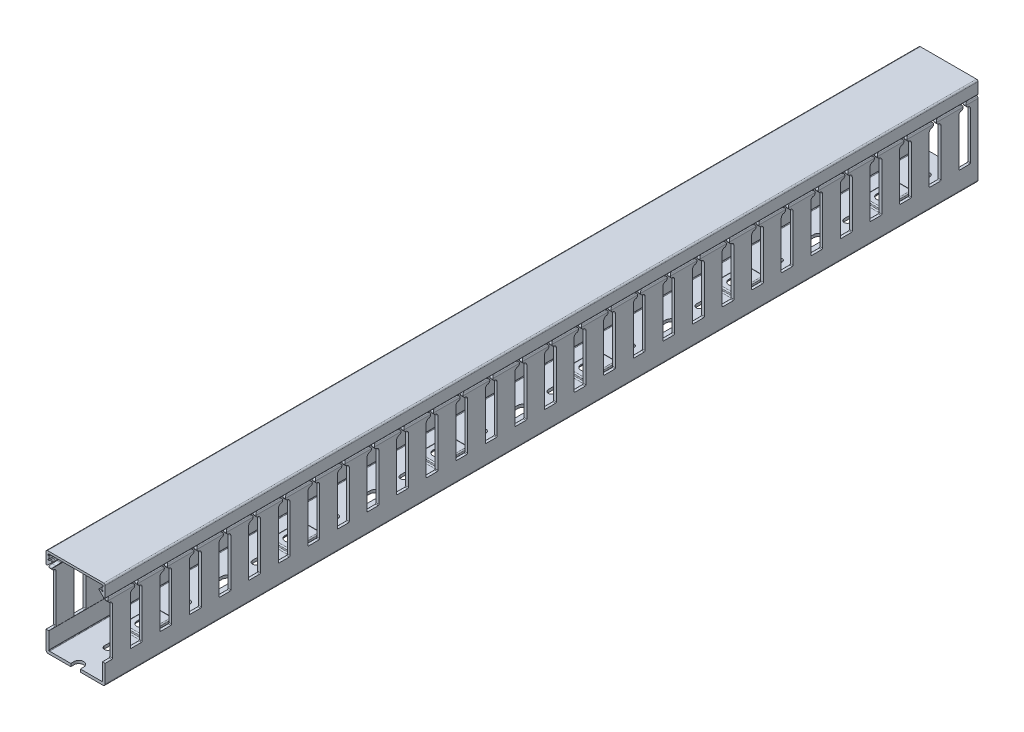
SolidWorks part; units mm, degrees
ref_plane "Front Plane" through (0, 0, 0) normal (0, 0, 1) x (1, 0, 0)
ref_plane "Top Plane" through (0, 0, 0) normal (0, 1, 0) x (1, 0, 0)
ref_plane "Right Plane" through (0, 0, 0) normal (1, 0, 0) x (0, 0, -1)
sketch "Sketch1" plane through (0, 0, 0) normal (0, 0, 1) x (1, 0, 0)
  line L0 (-18.2, -27.85) -> (-17.973, -27.983)
  line L1 (-20, -28.55) -> (-20, 19.1871)
  line L2 (-20, 21.7598) -> (-20, 29.05)
  line L3 (-18.5, 28.35) -> (-18.5, 27.55)
  line L4 (-18.5, 25.25) -> (-18.5, 25.058)
  line L5 (-19.6147, 20.1908) -> (-15.6798, 24.5609)
  line L6 (-17.8221, 24.7703) -> (-17.3671, 25.2097)
  line L7 (-15.9527, 24.4903) -> (-19.1527, 21.4001)
  line L8 (-18.1, 18.8416) -> (-18.1, -16.3923)
  line L9 (-18.1, -16.5077) -> (-18.1, -27.65)
  line L10 (-18, 25.55) -> (-18, 27.25)
  line L11 (-14.8603, 22.6316) -> (-17.9716, 19.1762)
  line L12 (-18.2, -16.45) -> (-18.1, -16.5077)
  line L13 (-13.3, 25.85) -> (-13.3, 24.6071)
  line L14 (-7, -28.15) -> (-7, -25.65)
  line L15 (-18.5, -30.05) -> (18.5, -30.05)
  line L16 (0, -30.05) -> (0, 30.05) construction
  line L18 (-17.6, -28.15) -> (17.6, -28.15)
  line L19 (-17.973, -27.983) -> (-17.973, -27.7208) construction
  line L20 (-18.082, -27.7829) -> (-17.973, -27.7208) construction
  line L21 (18.1, -16.5077) -> (18.1, -16.3923) construction
  line L23 (-7, -25.65) -> (7, -25.65)
  line L24 (-18.1, -16.5077) -> (-18.1, -16.3923) construction
  line L25 (-2.25, -30.05) -> (-2.25, -28.15)
  line L26 (2.25, -30.05) -> (2.25, -28.15)
  line L27 (7, -28.15) -> (7, -25.65)
  line L28 (17.973, -27.717) -> (18.082, -27.7829) construction
  line L29 (-18.1, -16.3923) -> (-18.2, -16.45)
  line L30 (18.1, -16.3923) -> (18.2, -16.45)
  line L31 (-18.082, -27.7829) -> (-18.2, -27.85)
  line L33 (18.4, 25.35) -> (18.2, 25.35)
  line L34 (-16.3, 25.35) -> (-17.0198, 25.35)
  line L35 (-18.4, 25.35) -> (-18.2, 25.35)
  line L36 (16.3, 25.35) -> (17.0198, 25.35)
  line L38 (-18.2, 27.45) -> (-18.4, 27.45)
  line L39 (18.2, 27.45) -> (18.4, 27.45)
  line L40 (16.0883, 27.65) -> (15.1, 27.65)
  line L41 (-16.0883, 27.65) -> (-15.1, 27.65)
  line L42 (-18.3, 28.55) -> (18.3, 28.55)
  line L44 (19, 30.05) -> (-19, 30.05)
  line L46 (-16.3812, 25.7055) -> (-17.6188, 25.3739)
  line L47 (16.3812, 25.7055) -> (17.6188, 25.3739)
  line L48 (13.3, 25.85) -> (13.3, 24.6071)
  line L49 (18, 25.55) -> (18, 27.25)
  line L50 (18.1, 18.8416) -> (18.1, -16.3923)
  line L51 (18.1, -16.5077) -> (18.1, -27.65)
  line L52 (18.5, 28.35) -> (18.5, 27.55)
  line L53 (18.5, 25.25) -> (18.5, 25.058)
  line L54 (18.2, -16.45) -> (18.1, -16.5077)
  line L55 (14.8603, 22.6316) -> (17.9716, 19.1762)
  line L56 (20, -28.55) -> (20, 19.1871)
  line L57 (20, 21.7598) -> (20, 29.05)
  line L58 (15.9527, 24.4903) -> (19.1527, 21.4001)
  line L59 (17.8221, 24.7703) -> (17.3671, 25.2097)
  line L60 (19.6147, 20.1908) -> (15.6798, 24.5609)
  line L61 (18.2, -27.85) -> (17.973, -27.983)
  line L62 (-2.25, -29.1) -> (2.25, -29.1) construction
  line L63 (-7, -26.9) -> (7, -26.9) construction
  line L64 (0, -29.1) -> (0, -26.9) construction
  line L68 (17.973, -27.983) -> (17.973, -27.717) construction
  line L69 (20, -4.6815) -> (18.1, -4.6815) construction
  line L70 (-20, -4.6815) -> (-18.1, -4.6815) construction
  line L71 (18.082, -27.7829) -> (18.2, -27.85)
  line L72 (16.4159, 20.9039) -> (17.8279, 22.1752) construction
  line L73 (18.2, -27.85) -> (17.973, -27.85) construction
  line L74 (20, 19.1871) -> (20, 19.7629) construction
  line L75 (20, 19.7629) -> (19.6147, 20.1908) construction
  line L76 (18.1, 18.8416) -> (18.1, 19.0335) construction
  line L77 (18.1, 19.0335) -> (17.9716, 19.1762) construction
  line L78 (20, 21.7598) -> (20, 20.5819) construction
  line L79 (20, 20.5819) -> (19.1527, 21.4001) construction
  line L80 (18.3, 28.55) -> (18.3, 30.05) construction
  line L81 (18.5, 28.35) -> (20, 28.35) construction
  line L82 (17.5946, 24.99) -> (16.5526, 23.911) construction
  line L83 (14.0985, 26.3171) -> (16.3812, 25.7055) construction
  line L84 (14.0985, 26.3171) -> (15.6798, 24.5609) construction
  line L85 (15.1, 24.6071) -> (15.1, 25.85) construction
  line L86 (15.1, 25.85) -> (16.0883, 25.85) construction
  line L87 (16.0883, 25.85) -> (16.0883, 24.6071) construction
  line L88 (16.0883, 24.6071) -> (15.1, 24.6071) construction
  arc A0 (-20, -28.55) -> (-18.5, -30.05) centre (-18.5, -28.55) ccw
  arc A1 (-18.1, -27.65) -> (-18.082, -27.7829) centre (-17.6, -27.65) ccw
  arc A2 (-17.973, -27.983) -> (-17.6, -28.15) centre (-17.6, -27.65) ccw
  arc A3 (-17.5208, 26.94) -> (-18.1276, 26.6686) centre (-15.7875, 22.25) ccw
  arc A4 (-14.8603, 22.6316) -> (-13.7623, 23.4026) centre (-15.9918, 25.41) ccw
  arc A5 (-16.0883, 27.65) -> (-17.5208, 26.94) centre (-16.0883, 25.85) ccw
  arc A6 (-13.3, 25.85) -> (-15.1, 27.65) centre (-15.1, 25.85) ccw
  arc A7 (-13.7623, 23.4026) -> (-13.3, 24.6071) centre (-15.1, 24.6071) ccw
  arc A8 (-19.6147, 20.1908) -> (-20, 19.1871) centre (-18.5, 19.1871) ccw
  arc A9 (-19, 30.05) -> (-20, 29.05) centre (-19, 29.05) ccw
  arc A10 (-15.6798, 24.5609) -> (-16.3812, 25.7055) centre (-16.2, 25.0293) ccw
  arc A11 (-18.1276, 26.6686) -> (-17.6188, 25.3739) centre (-17.8, 26.05) ccw
  arc A12 (-17.0198, 25.35) -> (-17.3671, 25.2097) centre (-17.0198, 24.85) ccw
  arc A13 (-15.9527, 24.4903) -> (-16.3, 25.35) centre (-16.3, 24.85) ccw
  arc A14 (-20, 21.7598) -> (-19.1527, 21.4001) centre (-19.5, 21.7598) ccw
  arc A15 (-17.9716, 19.1762) -> (-18.1, 18.8416) centre (-17.6, 18.8416) ccw
  arc A16 (-18.5, 25.058) -> (-17.8221, 24.7703) centre (-18.1, 25.058) ccw
  arc A17 (-18.3, 28.55) -> (-18.5, 28.35) centre (-18.3, 28.35) ccw
  arc A18 (-18, 27.25) -> (-18.2, 27.45) centre (-18.2, 27.25) ccw
  arc A19 (-18.2, 25.35) -> (-18, 25.55) centre (-18.2, 25.55) ccw
  arc A20 (-18.4, 25.35) -> (-18.5, 25.25) centre (-18.4, 25.25) ccw
  arc A21 (-18.5, 27.55) -> (-18.4, 27.45) centre (-18.4, 27.55) ccw
  arc A22 (18.5, -30.05) -> (20, -28.55) centre (18.5, -28.55) ccw
  arc A23 (17.6, -28.15) -> (17.973, -27.983) centre (17.6, -27.65) ccw
  arc A24 (18.082, -27.7829) -> (18.1, -27.65) centre (17.6, -27.65) ccw
  arc A25 (18.1276, 26.6686) -> (17.5208, 26.94) centre (15.7875, 22.25) ccw
  arc A26 (13.7623, 23.4026) -> (14.8603, 22.6316) centre (15.9918, 25.41) ccw
  arc A27 (13.3, 24.6071) -> (13.7623, 23.4026) centre (15.1, 24.6071) ccw
  arc A28 (15.1, 27.65) -> (13.3, 25.85) centre (15.1, 25.85) ccw
  arc A29 (17.5208, 26.94) -> (16.0883, 27.65) centre (16.0883, 25.85) ccw
  arc A30 (20, 19.1871) -> (19.6147, 20.1908) centre (18.5, 19.1871) ccw
  arc A31 (20, 29.05) -> (19, 30.05) centre (19, 29.05) ccw
  arc A32 (17.6188, 25.3739) -> (18.1276, 26.6686) centre (17.8, 26.05) ccw
  arc A33 (16.3812, 25.7055) -> (15.6798, 24.5609) centre (16.2, 25.0293) ccw
  arc A34 (17.3671, 25.2097) -> (17.0198, 25.35) centre (17.0198, 24.85) ccw
  arc A35 (16.3, 25.35) -> (15.9527, 24.4903) centre (16.3, 24.85) ccw
  arc A36 (19.1527, 21.4001) -> (20, 21.7598) centre (19.5, 21.7598) ccw
  arc A37 (18.1, 18.8416) -> (17.9716, 19.1762) centre (17.6, 18.8416) ccw
  arc A38 (17.8221, 24.7703) -> (18.5, 25.058) centre (18.1, 25.058) ccw
  arc A39 (18.5, 28.35) -> (18.3, 28.55) centre (18.3, 28.35) ccw
  arc A40 (18.2, 27.45) -> (18, 27.25) centre (18.2, 27.25) ccw
  arc A41 (18, 25.55) -> (18.2, 25.35) centre (18.2, 25.55) ccw
  arc A42 (18.5, 25.25) -> (18.4, 25.35) centre (18.4, 25.25) ccw
  arc A43 (18.4, 27.45) -> (18.5, 27.55) centre (18.4, 27.55) ccw
  point P188 (0, 28.55)
  dimension "D2" = 1.5
  dimension "D9" = 0.5
  dimension "D12" = 1
  dimension "D13" = 1.8
  dimension "D14" = 0.2
  dimension "D15" = 0.1
  dimension "D16" = 0.7
  dimension "D28" = 0.4
  dimension "D29" = 3
  dimension "D30" = 5
  dimension "D1" = 14
  dimension "Height" = 60.1
  dimension "Width" = 40
  dimension "D3" = 1.9
  dimension "D4" = 1.5
  dimension "D5" = 0.1155
  dimension "D6" = 46
  dimension "D7" = 138
  dimension "D10" = 2.5
  dimension "D11" = 4.5
  dimension "D18" = 0.3
  dimension "D19" = 0.266
  dimension "D20" = 60
  dimension "D21" = 8.6165
  dimension "D22" = 9.4681
  dimension "D23" = 0.5
  dimension "D24" = 1.1
  dimension "D25" = 2.1
  dimension "D26" = 0.9
  dimension "D27" = 4.8
  dimension "D31" = 0.9883
  dimension "D32" = 1.2429
  dimension "D33" = 33
  dimension "D34" = 5.0184
  dimension "D35" = 4.2208
  dimension "Slot Height" = 13.6
sketch "Sketch2" plane through (0, 0, 0) normal (0, 1, 0) x (1, 0, 0)
  line L1 (-20, 295) -> (20, 295)
  line L2 (-20, 295) -> (-20, -295)
  line L3 (-20, -295) -> (20, -295)
  line L4 (20, 295) -> (20, -295)
  line L5 (-20, 295) -> (20, -295) construction
  line L6 (-20, -295) -> (20, 295) construction
  line L9 (0, -300.25) -> (0, -292.75) construction
  line L10 (-3.25, -300.25) -> (-3.25, -292.75)
  line L11 (3.25, -300.25) -> (3.25, -292.75)
  line L15 (0, -289.5) -> (0, -292.75) construction
  line L16 (0, -300.25) -> (0, -303.5) construction
  line L17 (0, -273.25) -> (0, -269.75) construction
  line L18 (-2.25, -273.25) -> (-2.25, -269.75)
  line L19 (2.25, -273.25) -> (2.25, -269.75)
  line L23 (0, -273.25) -> (0, -275.5) construction
  line L24 (0, -250.25) -> (0, -242.75) construction
  line L26 (0, -269.75) -> (0, -267.5) construction
  line L30 (7, -257.2071) -> (-7, -257.2071)
  line L31 (7, -257.2071) -> (7, -235.7929)
  line L32 (7, -235.7929) -> (-7, -235.7929)
  line L33 (-7, -257.2071) -> (-7, -235.7929)
  line L34 (-3.25, -250.25) -> (-3.25, -242.75)
  line L35 (3.25, -250.25) -> (3.25, -242.75)
  line L36 (0, -200.25) -> (0, -192.75) construction
  line L37 (-3.25, -200.25) -> (-3.25, -192.75)
  line L38 (3.25, -200.25) -> (3.25, -192.75)
  line L45 (0, -223.25) -> (0, -219.75) construction
  line L46 (-2.25, -223.25) -> (-2.25, -219.75)
  line L47 (2.25, -223.25) -> (2.25, -219.75)
  arc A2 (-3.25, -300.25) -> (3.25, -300.25) centre (0, -300.25) ccw
  arc A3 (3.25, -292.75) -> (-3.25, -292.75) centre (0, -292.75) ccw
  arc A6 (-2.25, -273.25) -> (2.25, -273.25) centre (0, -273.25) ccw
  arc A7 (2.25, -269.75) -> (-2.25, -269.75) centre (0, -269.75) ccw
  arc A10 (-3.25, -250.25) -> (3.25, -250.25) centre (0, -250.25) ccw
  arc A11 (3.25, -242.75) -> (-3.25, -242.75) centre (0, -242.75) ccw
  arc A12 (-3.25, -200.25) -> (3.25, -200.25) centre (0, -200.25) ccw
  arc A13 (3.25, -192.75) -> (-3.25, -192.75) centre (0, -192.75) ccw
  arc A18 (-2.25, -223.25) -> (2.25, -223.25) centre (0, -223.25) ccw
  arc A19 (2.25, -219.75) -> (-2.25, -219.75) centre (0, -219.75) ccw
  point P0 (0, 0)
  point P14 (0, -296.5)
  point P33 (0, -271.5)
  point P67 (0, -246.5)
  point P74 (-7, -246.5)
  point P75 (0, -196.5)
  point P96 (0, -221.5)
  dimension "D1" = 5.5
  dimension "D2" = 14
  dimension "Length" = 590
  dimension "D3" = 6.5
  dimension "D4" = 8
  dimension "D5" = 23.5
  dimension "D6" = 21.4142
  dimension "D7" = 25
  dimension "Slot Spacing 2" = 100
  dimension "Slot Spacing 1" = 50
sketch "Sketch3" plane through (0, 0, 0) normal (0, 0, 1) x (1, 0, 0)
  line L0 (15.9527, 24.4903) -> (19.1527, 21.4001) construction
  line L1 (16.3, 25.35) -> (17.0198, 25.35) construction
  line L2 (17.8221, 24.7703) -> (17.3671, 25.2097) construction
  line L3 (18.5, 25.25) -> (18.5, 25.058) construction
  line L4 (18.4, 25.35) -> (18.2, 25.35) construction
  line L5 (18, 25.55) -> (18, 27.25) construction
  line L6 (18.2, 27.45) -> (18.4, 27.45) construction
  line L7 (18.5, 28.35) -> (18.5, 27.55) construction
  line L8 (20, 21.7598) -> (20, 29.05) construction
  line L9 (19, 30.05) -> (-19, 30.05) construction
  line L10 (-18.3, 28.55) -> (18.3, 28.55) construction
  line L11 (-18.5, 28.35) -> (-18.5, 27.55) construction
  line L12 (-18.2, 27.45) -> (-18.4, 27.45) construction
  line L13 (-18, 25.55) -> (-18, 27.25) construction
  line L14 (-18.4, 25.35) -> (-18.2, 25.35) construction
  line L15 (-18.5, 25.25) -> (-18.5, 25.058) construction
  line L16 (-17.8221, 24.7703) -> (-17.3671, 25.2097) construction
  line L17 (-16.3, 25.35) -> (-17.0198, 25.35) construction
  line L18 (-15.9527, 24.4903) -> (-19.1527, 21.4001) construction
  line L19 (-20, 21.7598) -> (-20, 29.05) construction
  line L20 (15.9527, 24.4903) -> (19.1527, 21.4001)
  line L21 (16.3, 25.35) -> (17.0198, 25.35)
  line L22 (17.8221, 24.7703) -> (17.3671, 25.2097)
  line L23 (18.5, 25.25) -> (18.5, 25.058)
  line L24 (18.4, 25.35) -> (18.2, 25.35)
  line L25 (18, 25.55) -> (18, 27.25)
  line L26 (18.2, 27.45) -> (18.4, 27.45)
  line L27 (18.5, 28.35) -> (18.5, 27.55)
  line L28 (20, 21.7598) -> (20, 29.05)
  line L29 (19, 30.05) -> (-19, 30.05)
  line L30 (-18.3, 28.55) -> (18.3, 28.55)
  line L31 (-18.5, 28.35) -> (-18.5, 27.55)
  line L32 (-18.2, 27.45) -> (-18.4, 27.45)
  line L33 (-18, 25.55) -> (-18, 27.25)
  line L34 (-18.4, 25.35) -> (-18.2, 25.35)
  line L35 (-18.5, 25.25) -> (-18.5, 25.058)
  line L36 (-17.8221, 24.7703) -> (-17.3671, 25.2097)
  line L37 (-16.3, 25.35) -> (-17.0198, 25.35)
  line L38 (-15.9527, 24.4903) -> (-19.1527, 21.4001)
  line L39 (-20, 21.7598) -> (-20, 29.05)
  arc A0 (19.1527, 21.4001) -> (20, 21.7598) centre (19.5, 21.7598) ccw construction
  arc A1 (16.3, 25.35) -> (15.9527, 24.4903) centre (16.3, 24.85) ccw construction
  arc A2 (17.3671, 25.2097) -> (17.0198, 25.35) centre (17.0198, 24.85) ccw construction
  arc A3 (17.8221, 24.7703) -> (18.5, 25.058) centre (18.1, 25.058) ccw construction
  arc A4 (18.5, 25.25) -> (18.4, 25.35) centre (18.4, 25.25) ccw construction
  arc A5 (18, 25.55) -> (18.2, 25.35) centre (18.2, 25.55) ccw construction
  arc A6 (18.2, 27.45) -> (18, 27.25) centre (18.2, 27.25) ccw construction
  arc A7 (18.4, 27.45) -> (18.5, 27.55) centre (18.4, 27.55) ccw construction
  arc A8 (18.5, 28.35) -> (18.3, 28.55) centre (18.3, 28.35) ccw construction
  arc A9 (20, 29.05) -> (19, 30.05) centre (19, 29.05) ccw construction
  arc A10 (-18.3, 28.55) -> (-18.5, 28.35) centre (-18.3, 28.35) ccw construction
  arc A11 (-18.5, 27.55) -> (-18.4, 27.45) centre (-18.4, 27.55) ccw construction
  arc A12 (-18, 27.25) -> (-18.2, 27.45) centre (-18.2, 27.25) ccw construction
  arc A13 (-18.2, 25.35) -> (-18, 25.55) centre (-18.2, 25.55) ccw construction
  arc A14 (-18.4, 25.35) -> (-18.5, 25.25) centre (-18.4, 25.25) ccw construction
  arc A15 (-18.5, 25.058) -> (-17.8221, 24.7703) centre (-18.1, 25.058) ccw construction
  arc A16 (-17.0198, 25.35) -> (-17.3671, 25.2097) centre (-17.0198, 24.85) ccw construction
  arc A17 (-15.9527, 24.4903) -> (-16.3, 25.35) centre (-16.3, 24.85) ccw construction
  arc A18 (-20, 21.7598) -> (-19.1527, 21.4001) centre (-19.5, 21.7598) ccw construction
  arc A19 (-19, 30.05) -> (-20, 29.05) centre (-19, 29.05) ccw construction
  arc A20 (19.1527, 21.4001) -> (20, 21.7598) centre (19.5, 21.7598) ccw
  arc A21 (16.3, 25.35) -> (15.9527, 24.4903) centre (16.3, 24.85) ccw
  arc A22 (17.3671, 25.2097) -> (17.0198, 25.35) centre (17.0198, 24.85) ccw
  arc A23 (17.8221, 24.7703) -> (18.5, 25.058) centre (18.1, 25.058) ccw
  arc A24 (18.5, 25.25) -> (18.4, 25.35) centre (18.4, 25.25) ccw
  arc A25 (18, 25.55) -> (18.2, 25.35) centre (18.2, 25.55) ccw
  arc A26 (18.2, 27.45) -> (18, 27.25) centre (18.2, 27.25) ccw
  arc A27 (18.4, 27.45) -> (18.5, 27.55) centre (18.4, 27.55) ccw
  arc A28 (18.5, 28.35) -> (18.3, 28.55) centre (18.3, 28.35) ccw
  arc A29 (20, 29.05) -> (19, 30.05) centre (19, 29.05) ccw
  arc A30 (-18.3, 28.55) -> (-18.5, 28.35) centre (-18.3, 28.35) ccw
  arc A31 (-18.5, 27.55) -> (-18.4, 27.45) centre (-18.4, 27.55) ccw
  arc A32 (-18, 27.25) -> (-18.2, 27.45) centre (-18.2, 27.25) ccw
  arc A33 (-18.2, 25.35) -> (-18, 25.55) centre (-18.2, 25.55) ccw
  arc A34 (-18.4, 25.35) -> (-18.5, 25.25) centre (-18.4, 25.25) ccw
  arc A35 (-18.5, 25.058) -> (-17.8221, 24.7703) centre (-18.1, 25.058) ccw
  arc A36 (-17.0198, 25.35) -> (-17.3671, 25.2097) centre (-17.0198, 24.85) ccw
  arc A37 (-15.9527, 24.4903) -> (-16.3, 25.35) centre (-16.3, 24.85) ccw
  arc A38 (-20, 21.7598) -> (-19.1527, 21.4001) centre (-19.5, 21.7598) ccw
  arc A39 (-19, 30.05) -> (-20, 29.05) centre (-19, 29.05) ccw
extrude "Boss-Extrude1" add sketch "Sketch3" along normal up to vertex (295 mm away) from vertex at -295 separate body starting at point (20, 0, -295)
sketch "Sketch4" plane through (0, 0, 0) normal (0, 0, 1) x (1, 0, 0)
  line L0 (18.2, -27.85) -> (17.973, -27.983) construction
  line L1 (18.082, -27.7829) -> (18.2, -27.85) construction
  line L2 (18.1, -16.5077) -> (18.1, -27.65) construction
  line L3 (18.2, -16.45) -> (18.1, -16.5077) construction
  line L4 (18.1, -16.3923) -> (18.2, -16.45) construction
  line L5 (20, -28.55) -> (20, 19.1871) construction
  line L6 (18.1, 18.8416) -> (18.1, -16.3923) construction
  line L7 (19.6147, 20.1908) -> (15.6798, 24.5609) construction
  line L8 (16.3812, 25.7055) -> (17.6188, 25.3739) construction
  line L9 (14.8603, 22.6316) -> (17.9716, 19.1762) construction
  line L10 (13.3, 25.85) -> (13.3, 24.6071) construction
  line L11 (16.0883, 27.65) -> (15.1, 27.65) construction
  line L12 (-16.3812, 25.7055) -> (-17.6188, 25.3739) construction
  line L13 (-16.0883, 27.65) -> (-15.1, 27.65) construction
  line L14 (-13.3, 25.85) -> (-13.3, 24.6071) construction
  line L15 (-19.6147, 20.1908) -> (-15.6798, 24.5609) construction
  line L16 (-14.8603, 22.6316) -> (-17.9716, 19.1762) construction
  line L17 (-18.1, 18.8416) -> (-18.1, -16.3923) construction
  line L18 (-18.1, -16.3923) -> (-18.2, -16.45) construction
  line L19 (-18.2, -16.45) -> (-18.1, -16.5077) construction
  line L20 (-18.1, -16.5077) -> (-18.1, -27.65) construction
  line L21 (-18.082, -27.7829) -> (-18.2, -27.85) construction
  line L22 (-18.2, -27.85) -> (-17.973, -27.983) construction
  line L23 (-17.6, -28.15) -> (17.6, -28.15) construction
  line L24 (-18.5, -30.05) -> (18.5, -30.05) construction
  line L25 (-20, -28.55) -> (-20, 19.1871) construction
  line L26 (18.2, -27.85) -> (17.973, -27.983)
  line L27 (18.082, -27.7829) -> (18.2, -27.85)
  line L28 (18.1, -16.5077) -> (18.1, -27.65)
  line L29 (18.2, -16.45) -> (18.1, -16.5077)
  line L30 (18.1, -16.3923) -> (18.2, -16.45)
  line L31 (20, -28.55) -> (20, 19.1871)
  line L32 (18.1, 18.8416) -> (18.1, -16.3923)
  line L33 (19.6147, 20.1908) -> (15.6798, 24.5609)
  line L34 (16.3812, 25.7055) -> (17.6188, 25.3739)
  line L35 (14.8603, 22.6316) -> (17.9716, 19.1762)
  line L36 (13.3, 25.85) -> (13.3, 24.6071)
  line L37 (16.0883, 27.65) -> (15.1, 27.65)
  line L38 (-16.3812, 25.7055) -> (-17.6188, 25.3739)
  line L39 (-16.0883, 27.65) -> (-15.1, 27.65)
  line L40 (-13.3, 25.85) -> (-13.3, 24.6071)
  line L41 (-19.6147, 20.1908) -> (-15.6798, 24.5609)
  line L42 (-14.8603, 22.6316) -> (-17.9716, 19.1762)
  line L43 (-18.1, 18.8416) -> (-18.1, -16.3923)
  line L44 (-18.1, -16.3923) -> (-18.2, -16.45)
  line L45 (-18.2, -16.45) -> (-18.1, -16.5077)
  line L46 (-18.1, -16.5077) -> (-18.1, -27.65)
  line L47 (-18.082, -27.7829) -> (-18.2, -27.85)
  line L48 (-18.2, -27.85) -> (-17.973, -27.983)
  line L49 (-17.6, -28.15) -> (17.6, -28.15)
  line L50 (-18.5, -30.05) -> (18.5, -30.05)
  line L51 (-20, -28.55) -> (-20, 19.1871)
  arc A0 (18.5, -30.05) -> (20, -28.55) centre (18.5, -28.55) ccw construction
  arc A1 (17.6, -28.15) -> (17.973, -27.983) centre (17.6, -27.65) ccw construction
  arc A2 (18.082, -27.7829) -> (18.1, -27.65) centre (17.6, -27.65) ccw construction
  arc A3 (18.1, 18.8416) -> (17.9716, 19.1762) centre (17.6, 18.8416) ccw construction
  arc A4 (20, 19.1871) -> (19.6147, 20.1908) centre (18.5, 19.1871) ccw construction
  arc A5 (16.3812, 25.7055) -> (15.6798, 24.5609) centre (16.2, 25.0293) ccw construction
  arc A6 (13.7623, 23.4026) -> (14.8603, 22.6316) centre (15.9918, 25.41) ccw construction
  arc A7 (13.3, 24.6071) -> (13.7623, 23.4026) centre (15.1, 24.6071) ccw construction
  arc A8 (15.1, 27.65) -> (13.3, 25.85) centre (15.1, 25.85) ccw construction
  arc A9 (17.5208, 26.94) -> (16.0883, 27.65) centre (16.0883, 25.85) ccw construction
  arc A10 (18.1276, 26.6686) -> (17.5208, 26.94) centre (15.7875, 22.25) ccw construction
  arc A11 (17.6188, 25.3739) -> (18.1276, 26.6686) centre (17.8, 26.05) ccw construction
  arc A12 (-15.6798, 24.5609) -> (-16.3812, 25.7055) centre (-16.2, 25.0293) ccw construction
  arc A13 (-18.1276, 26.6686) -> (-17.6188, 25.3739) centre (-17.8, 26.05) ccw construction
  arc A14 (-17.5208, 26.94) -> (-18.1276, 26.6686) centre (-15.7875, 22.25) ccw construction
  arc A15 (-16.0883, 27.65) -> (-17.5208, 26.94) centre (-16.0883, 25.85) ccw construction
  arc A16 (-13.3, 25.85) -> (-15.1, 27.65) centre (-15.1, 25.85) ccw construction
  arc A17 (-13.7623, 23.4026) -> (-13.3, 24.6071) centre (-15.1, 24.6071) ccw construction
  arc A18 (-14.8603, 22.6316) -> (-13.7623, 23.4026) centre (-15.9918, 25.41) ccw construction
  arc A19 (-17.9716, 19.1762) -> (-18.1, 18.8416) centre (-17.6, 18.8416) ccw construction
  arc A20 (-19.6147, 20.1908) -> (-20, 19.1871) centre (-18.5, 19.1871) ccw construction
  arc A21 (-18.1, -27.65) -> (-18.082, -27.7829) centre (-17.6, -27.65) ccw construction
  arc A22 (-17.973, -27.983) -> (-17.6, -28.15) centre (-17.6, -27.65) ccw construction
  arc A23 (-20, -28.55) -> (-18.5, -30.05) centre (-18.5, -28.55) ccw construction
  arc A24 (18.5, -30.05) -> (20, -28.55) centre (18.5, -28.55) ccw
  arc A25 (17.6, -28.15) -> (17.973, -27.983) centre (17.6, -27.65) ccw
  arc A26 (18.082, -27.7829) -> (18.1, -27.65) centre (17.6, -27.65) ccw
  arc A27 (18.1, 18.8416) -> (17.9716, 19.1762) centre (17.6, 18.8416) ccw
  arc A28 (20, 19.1871) -> (19.6147, 20.1908) centre (18.5, 19.1871) ccw
  arc A29 (16.3812, 25.7055) -> (15.6798, 24.5609) centre (16.2, 25.0293) ccw
  arc A30 (13.7623, 23.4026) -> (14.8603, 22.6316) centre (15.9918, 25.41) ccw
  arc A31 (13.3, 24.6071) -> (13.7623, 23.4026) centre (15.1, 24.6071) ccw
  arc A32 (15.1, 27.65) -> (13.3, 25.85) centre (15.1, 25.85) ccw
  arc A33 (17.5208, 26.94) -> (16.0883, 27.65) centre (16.0883, 25.85) ccw
  arc A34 (18.1276, 26.6686) -> (17.5208, 26.94) centre (15.7875, 22.25) ccw
  arc A35 (17.6188, 25.3739) -> (18.1276, 26.6686) centre (17.8, 26.05) ccw
  arc A36 (-15.6798, 24.5609) -> (-16.3812, 25.7055) centre (-16.2, 25.0293) ccw
  arc A37 (-18.1276, 26.6686) -> (-17.6188, 25.3739) centre (-17.8, 26.05) ccw
  arc A38 (-17.5208, 26.94) -> (-18.1276, 26.6686) centre (-15.7875, 22.25) ccw
  arc A39 (-16.0883, 27.65) -> (-17.5208, 26.94) centre (-16.0883, 25.85) ccw
  arc A40 (-13.3, 25.85) -> (-15.1, 27.65) centre (-15.1, 25.85) ccw
  arc A41 (-13.7623, 23.4026) -> (-13.3, 24.6071) centre (-15.1, 24.6071) ccw
  arc A42 (-14.8603, 22.6316) -> (-13.7623, 23.4026) centre (-15.9918, 25.41) ccw
  arc A43 (-17.9716, 19.1762) -> (-18.1, 18.8416) centre (-17.6, 18.8416) ccw
  arc A44 (-19.6147, 20.1908) -> (-20, 19.1871) centre (-18.5, 19.1871) ccw
  arc A45 (-18.1, -27.65) -> (-18.082, -27.7829) centre (-17.6, -27.65) ccw
  arc A46 (-17.973, -27.983) -> (-17.6, -28.15) centre (-17.6, -27.65) ccw
  arc A47 (-20, -28.55) -> (-18.5, -30.05) centre (-18.5, -28.55) ccw
extrude "Boss-Extrude2" add sketch "Sketch4" along normal up to vertex (295 mm away) from vertex at -295 separate body starting at point (20, 0, -295)
sketch "Sketch5" plane through (0, 0, 0) normal (0, 1, 0) x (1, 0, 0)
  line L4 (7, -235.7929) -> (-7, -235.7929) construction
  line L5 (7, -257.2071) -> (7, -235.7929) construction
  line L6 (7, -257.2071) -> (-7, -257.2071) construction
  line L7 (-7, -257.2071) -> (-7, -235.7929) construction
  line L12 (7, -235.7929) -> (-7, -235.7929)
  line L13 (7, -257.2071) -> (7, -235.7929)
  line L14 (7, -257.2071) -> (-7, -257.2071)
  line L15 (-7, -257.2071) -> (-7, -235.7929)
extrude "Boss-Extrude3" add sketch "Sketch5" along normal up to vertex (-25.65 mm away) from vertex at -30.05 starting at point (0, -30.05, 0)
sketch "Sketch6" plane through (0, 0, 0) normal (0, 1, 0) x (1, 0, 0)
  line L4 (-7, -257.2071) -> (-7, -235.7929) construction
  line L5 (7, -235.7929) -> (-7, -235.7929) construction
  line L6 (7, -257.2071) -> (7, -235.7929) construction
  line L7 (7, -257.2071) -> (-7, -257.2071) construction
  line L12 (-7, -257.2071) -> (-7, -235.7929) construction
  line L13 (7, -235.7929) -> (-7, -235.7929) construction
  line L14 (7, -257.2071) -> (7, -235.7929) construction
  line L15 (7, -257.2071) -> (-7, -257.2071) construction
  line L16 (6.268, -256.4751) -> (6.268, -236.5249)
  line L17 (6.268, -236.5249) -> (-6.268, -236.5249)
  line L18 (-6.268, -256.4751) -> (-6.268, -236.5249)
  line L19 (6.268, -256.4751) -> (-6.268, -256.4751)
  dimension "D1" = 0.732
extrude "Cut-Extrude1" cut sketch "Sketch6" along normal blind 3.6678 from vertex at -30.05 starting at point (0, -30.05, 0)
fillet "Fillet1" radius 0.732 24 edges at (0, -28.15, 235.7929) (7, -26.9, 235.7929) (7, -28.15, 246.5) (-7, -28.15, 246.5) (-7, -26.9, 235.7929) (7, -26.9, 257.2071) (0, -28.15, 257.2071) (-7, -26.9, 257.2071) (0, -25.65, 257.2071) (-7, -25.65, 246.5) (0, -25.65, 235.7929) (7, -25.65, 246.5) (0, -26.3822, 236.5249) (0, -30.05, 236.5249) (-6.268, -26.3822, 246.5) (-6.268, -30.05, 246.5) (0, -26.3822, 256.4751) (0, -30.05, 256.4751) (6.268, -26.3822, 246.5) (6.268, -30.05, 246.5) (-6.268, -28.2161, 236.5249) (-6.268, -28.2161, 256.4751) (6.268, -28.2161, 236.5249) (6.268, -28.2161, 256.4751)
pattern_linear "LPattern1" count 6 spacing 100 along (0, 0, -1) of "Boss-Extrude3", "Cut-Extrude1", "Fillet1"
sketch "Sketch7" plane through (0, 0, 0) normal (0, 1, 0) x (1, 0, 0)
  line L4 (-2.25, -223.25) -> (-2.25, -219.75) construction
  line L6 (-3.25, -250.25) -> (-3.25, -242.75) construction
  line L7 (-2.25, -273.25) -> (-2.25, -269.75) construction
  line L10 (-3.25, -300.25) -> (-3.25, -292.75) construction
  line L16 (-2.25, -223.25) -> (-2.25, -219.75)
  line L18 (-3.25, -250.25) -> (-3.25, -242.75)
  line L19 (-2.25, -273.25) -> (-2.25, -269.75)
  line L22 (-3.25, -300.25) -> (-3.25, -292.75)
  line L28 (2.25, -223.25) -> (2.25, -219.75) construction
  line L30 (3.25, -250.25) -> (3.25, -242.75) construction
  line L31 (2.25, -273.25) -> (2.25, -269.75) construction
  line L34 (3.25, -300.25) -> (3.25, -292.75) construction
  line L40 (2.25, -223.25) -> (2.25, -219.75)
  line L42 (3.25, -250.25) -> (3.25, -242.75)
  line L43 (2.25, -273.25) -> (2.25, -269.75)
  line L46 (3.25, -300.25) -> (3.25, -292.75)
  line L54 (0, -271.5) -> (0, -221.5) construction
  arc A8 (-2.25, -223.25) -> (2.25, -223.25) centre (0, -223.25) ccw construction
  arc A9 (2.25, -219.75) -> (-2.25, -219.75) centre (0, -219.75) ccw construction
  arc A12 (-3.25, -250.25) -> (3.25, -250.25) centre (0, -250.25) ccw construction
  arc A13 (3.25, -242.75) -> (-3.25, -242.75) centre (0, -242.75) ccw construction
  arc A14 (-2.25, -273.25) -> (2.25, -273.25) centre (0, -273.25) ccw construction
  arc A15 (2.25, -269.75) -> (-2.25, -269.75) centre (0, -269.75) ccw construction
  arc A20 (-3.25, -300.25) -> (3.25, -300.25) centre (0, -300.25) ccw construction
  arc A21 (3.25, -292.75) -> (-3.25, -292.75) centre (0, -292.75) ccw construction
  arc A32 (-2.25, -223.25) -> (2.25, -223.25) centre (0, -223.25) ccw
  arc A33 (2.25, -219.75) -> (-2.25, -219.75) centre (0, -219.75) ccw
  arc A36 (-3.25, -250.25) -> (3.25, -250.25) centre (0, -250.25) ccw
  arc A37 (3.25, -242.75) -> (-3.25, -242.75) centre (0, -242.75) ccw
  arc A38 (-2.25, -273.25) -> (2.25, -273.25) centre (0, -273.25) ccw
  arc A39 (2.25, -269.75) -> (-2.25, -269.75) centre (0, -269.75) ccw
  arc A44 (-3.25, -300.25) -> (3.25, -300.25) centre (0, -300.25) ccw
  arc A45 (3.25, -292.75) -> (-3.25, -292.75) centre (0, -292.75) ccw
extrude "Cut-Extrude2" cut sketch "Sketch7" against normal through all both and the other way through all
pattern_linear "LPattern2" count 7 spacing 100 along (0, 0, -1) of "Cut-Extrude2"
sketch "Sketch8" plane through (0, 0, 0) normal (1, 0, 0) x (0, 0, -1)
  line L0 (-298, 15.6859) -> (-298, -15.95)
  line L1 (-290, -15.95) -> (-290, 15.6859)
  line L2 (-296, 15.6859) -> (-292, 15.6859) construction
  line L3 (-297.5, -16.45) -> (-290.5, -16.45)
  line L4 (-292, 15.6859) -> (-292, 22.6141) construction
  line L5 (-292, 22.6141) -> (-296, 22.6141) construction
  line L6 (-298, 51.2859) -> (-298, 22.6141)
  line L7 (-290, 22.6141) -> (-290, 51.2859)
  line L9 (-296.5, 19.15) -> (-291.5, 19.15) construction
  line L11 (-296, 22.6141) -> (-296, 15.6859) construction
  line L13 (-298, 36.95) -> (-290, 36.95) construction
  line L15 (-298, 58.2141) -> (-298, 90.35)
  line L16 (-298, 90.35) -> (-290, 90.35)
  line L17 (-290, 90.35) -> (-290, 58.2141)
  line L18 (-291.5, 19.15) -> (-291.5, 54.75) construction
  line L19 (-291.5, 54.75) -> (-291.5, 90.35) construction
  line L20 (-291.5, 19.15) -> (-291.5, -16.45) construction
  arc A2 (-290.5, -16.45) -> (-290, -15.95) centre (-290.5, -15.95) ccw
  arc A3 (-298, -15.95) -> (-297.5, -16.45) centre (-297.5, -15.95) ccw
  arc A4 (-296.2857, 17.6654) -> (-298, 15.6859) centre (-296, 15.6859) ccw
  arc A5 (-298, 22.6141) -> (-296.2857, 20.6346) centre (-296, 22.6141) ccw
  arc A6 (-296.2857, 17.6654) -> (-296.2857, 20.6346) centre (-296.5, 19.15) ccw
  arc A9 (-291.7143, 17.6654) -> (-290, 15.6859) centre (-292, 15.6859) cw
  arc A11 (-291.7143, 17.6654) -> (-291.7143, 20.6346) centre (-291.5, 19.15) cw
  arc A14 (-290, 22.6141) -> (-291.7143, 20.6346) centre (-292, 22.6141) cw
  arc A15 (-290, 51.2859) -> (-291.7143, 53.2654) centre (-292, 51.2859) ccw
  arc A16 (-291.7143, 56.2346) -> (-291.7143, 53.2654) centre (-291.5, 54.75) ccw
  arc A17 (-291.7143, 56.2346) -> (-290, 58.2141) centre (-292, 58.2141) ccw
  arc A18 (-296.2857, 56.2346) -> (-298, 58.2141) centre (-296, 58.2141) cw
  arc A19 (-296.2857, 56.2346) -> (-296.2857, 53.2654) centre (-296.5, 54.75) cw
  arc A20 (-298, 51.2859) -> (-296.2857, 53.2654) centre (-296, 51.2859) cw
  point P36 (-214, -16.45)
  point P38 (-294, -16.45)
  point P40 (-234, -16.45)
  point P42 (-293, 19.15)
  point P45 (-295, 19.15)
  dimension "D3" = 0.5
  dimension "D4" = 2
  dimension "D5" = 1.5
  dimension "D1" = 8
  dimension "D2" = 6.9282
  dimension "D6" = 80
  dimension "D7" = 2
  dimension "D8" = 20
  dimension "Wire Slot Height Space" = 35.6
extrude "Cut-Extrude3" cut sketch "Sketch8" against normal through all both and the other way through all
pattern_linear "LPattern4" count 32 spacing 20 along (0, 0, -1) of "Cut-Extrude3"
equation "\"D3@LPattern1\"=\"Slot Spacing 2@Sketch2\""
equation "\"D1@LPattern1\"=Round(\"Length@Sketch2\"/\"Slot Spacing 2@Sketch2\")"
equation "\"D3@LPattern2\"=\"Slot Spacing 2@Sketch2\""
equation "\"D1@LPattern2\"=Round(\"Length@Sketch2\"/\"Slot Spacing 2@Sketch2\")+1"
equation "\"D1@LPattern4\"=Round(\"Length@Sketch2\"/\"D3@LPattern4\")+2"
